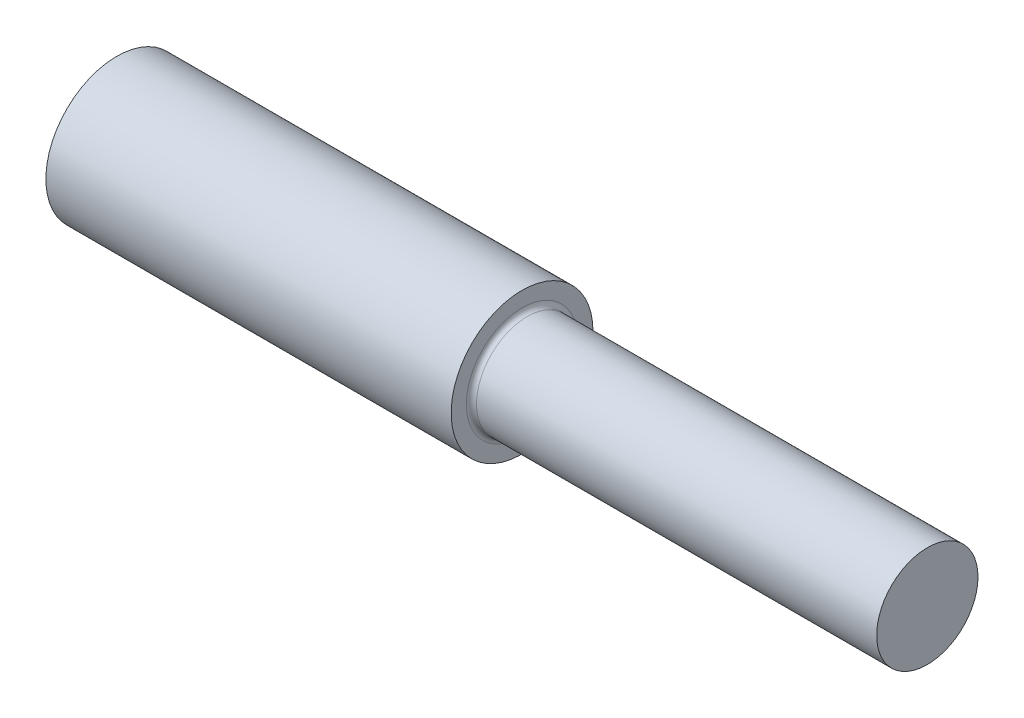
SolidWorks part; units mm, degrees
ref_plane "Front" through (0, 0, 0) normal (0, 0, 1) x (1, 0, 0)
ref_plane "Top" through (0, 0, 0) normal (0, 1, 0) x (1, 0, 0)
ref_plane "Right" through (0, 0, 0) normal (1, 0, 0) x (0, 0, -1)
sketch "Sketch1" plane through (0, 0, 0) normal (1, 0, 0) x (0, 0, -1)
  circle A0 centre (0, 0) radius 17.78
extrude "Large Dia Segment" add sketch "Sketch1" along normal blind 101.6
sketch "Sketch2" plane through (101.6, 0, 0) normal (1, 0, 0) x (0, 0, -1)
  circle A0 centre (0, 0) radius 12.7
extrude "Small Dia Segment" add sketch "Sketch2" along normal blind 101.6
fillet "Fillet 0.05 in" radius 1.27 1 edges at (101.6, 0, -12.7)
